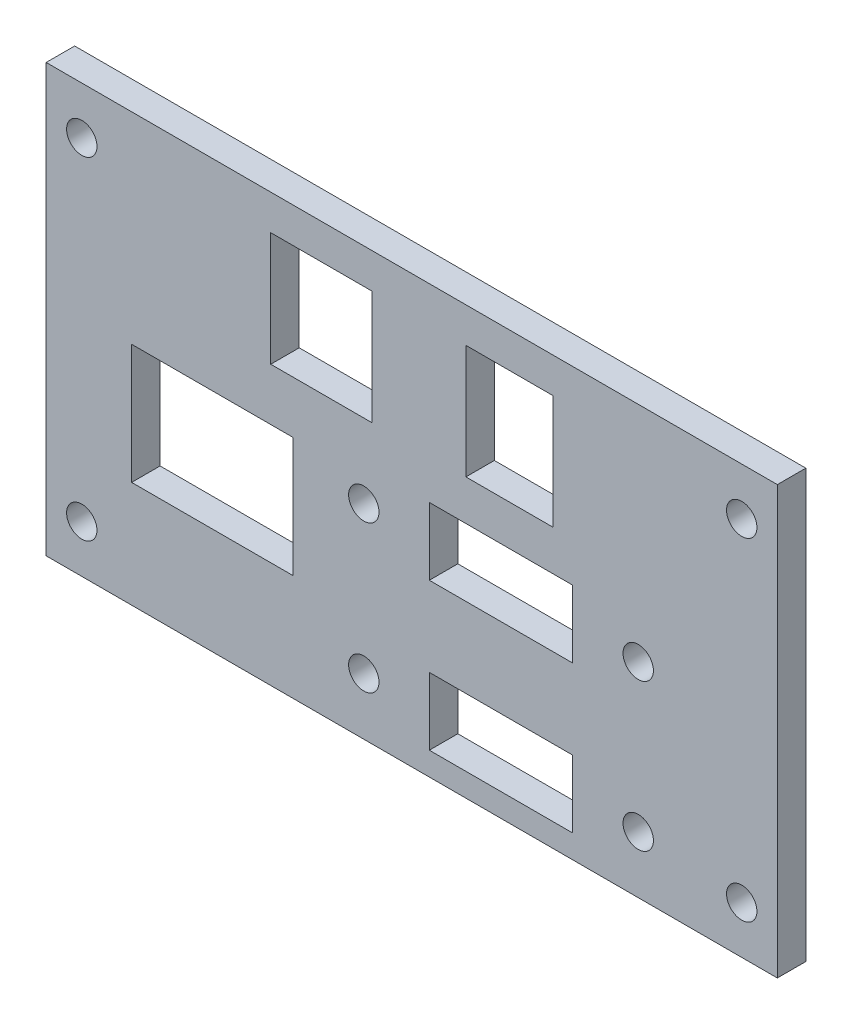
SolidWorks part; units mm, degrees
ref_plane "Alzado" through (0, 0, 0) normal (0, 0, 1) x (1, 0, 0)
ref_plane "Planta" through (0, 0, 0) normal (0, 1, 0) x (1, 0, 0)
ref_plane "Vista lateral" through (0, 0, 0) normal (1, 0, 0) x (0, 0, -1)
sketch "Croquis1" plane through (0, 0, 0) normal (0, 0, 1) x (1, 0, 0)
  line L1 (0, 0) -> (77, 0)
  line L2 (0, 0) -> (0, 45)
  line L3 (0, 45) -> (77, 45)
  line L4 (77, 0) -> (77, 45)
  dimension "D1" = 45
  dimension "D2" = 77
extrude "Saliente-Extruir1" add sketch "Croquis1" along normal blind 3
sketch "Croquis2" plane through (0, 0, 3) normal (0, 0, 1) x (1, 0, 0)
  line L0 (0, 22.5) -> (77, 22.5) construction
  line L1 (0, 45) -> (0, 0) construction
  line L2 (77, 0) -> (77, 45) construction
  line L3 (3.75, 40) -> (3.75, 22.5) construction
  line L4 (3.75, 22.5) -> (3.75, 5) construction
  line L5 (3.75, 5) -> (38.5, 22.5) construction
  line L6 (38.5, 22.5) -> (73.25, 40) construction
  line L7 (73.25, 40) -> (73.25, 22.5) construction
  line L8 (73.25, 22.5) -> (73.25, 5) construction
  line L9 (40.35, 6) -> (33.45, 6) construction
  line L10 (9, 23.8) -> (26, 23.8)
  line L11 (9, 23.8) -> (9, 11.2)
  line L12 (9, 11.2) -> (26, 11.2)
  line L13 (26, 23.8) -> (26, 11.2)
  line L14 (23.65, 41.3) -> (34.3, 41.3)
  line L15 (23.65, 41.3) -> (23.65, 29.3)
  line L16 (23.65, 29.3) -> (34.3, 29.3)
  line L17 (34.3, 41.3) -> (34.3, 29.3)
  line L18 (44.2, 41.3) -> (53.35, 41.3)
  line L19 (44.2, 41.3) -> (44.2, 29.3)
  line L20 (44.2, 29.3) -> (53.35, 29.3)
  line L21 (53.35, 41.3) -> (53.35, 29.3)
  line L22 (40.35, 25.05) -> (55.45, 25.05)
  line L23 (40.35, 25.05) -> (40.35, 17.95)
  line L24 (40.35, 17.95) -> (55.45, 17.95)
  line L25 (55.45, 25.05) -> (55.45, 17.95)
  line L26 (40.35, 2.45) -> (55.45, 2.45)
  line L27 (40.35, 2.45) -> (40.35, 9.55)
  line L28 (40.35, 9.55) -> (55.45, 9.55)
  line L29 (55.45, 2.45) -> (55.45, 9.55)
  line L30 (55.45, 6) -> (62.35, 6) construction
  line L31 (55.45, 21.5) -> (62.35, 21.5) construction
  line L32 (40.35, 21.5) -> (33.45, 21.5) construction
  line L33 (77, 45) -> (0, 45) construction
  line L34 (0, 0) -> (77, 0) construction
  circle A0 centre (3.75, 40) radius 1.6
  circle A1 centre (3.75, 5) radius 1.6
  circle A2 centre (73.25, 5) radius 1.6
  circle A3 centre (73.25, 40) radius 1.6
  circle A4 centre (33.45, 21.5) radius 1.6
  circle A5 centre (33.45, 6) radius 1.6
  circle A6 centre (62.35, 21.5) radius 1.6
  circle A7 centre (62.35, 6) radius 1.6
  dimension "D3" = 3.2
  dimension "D4" = 3.2
  dimension "D1" = 35
  dimension "D2" = 69.5
  dimension "D5" = 9
  dimension "D6" = 26
  dimension "D7" = 21.2
  dimension "D8" = 11.2
  dimension "D9" = 3.7
  dimension "D10" = 15.7
  dimension "D11" = 23.65
  dimension "D12" = 34.3
  dimension "D13" = 32.8
  dimension "D14" = 23.65
  dimension "D15" = 6
  dimension "D16" = 21.5
  dimension "D17" = 33.45
  dimension "D18" = 14.65
  dimension "D19" = 21.55
  dimension "D20" = 2.45
extrude "Cortar-Extruir1" cut sketch "Croquis2" against normal up to next
